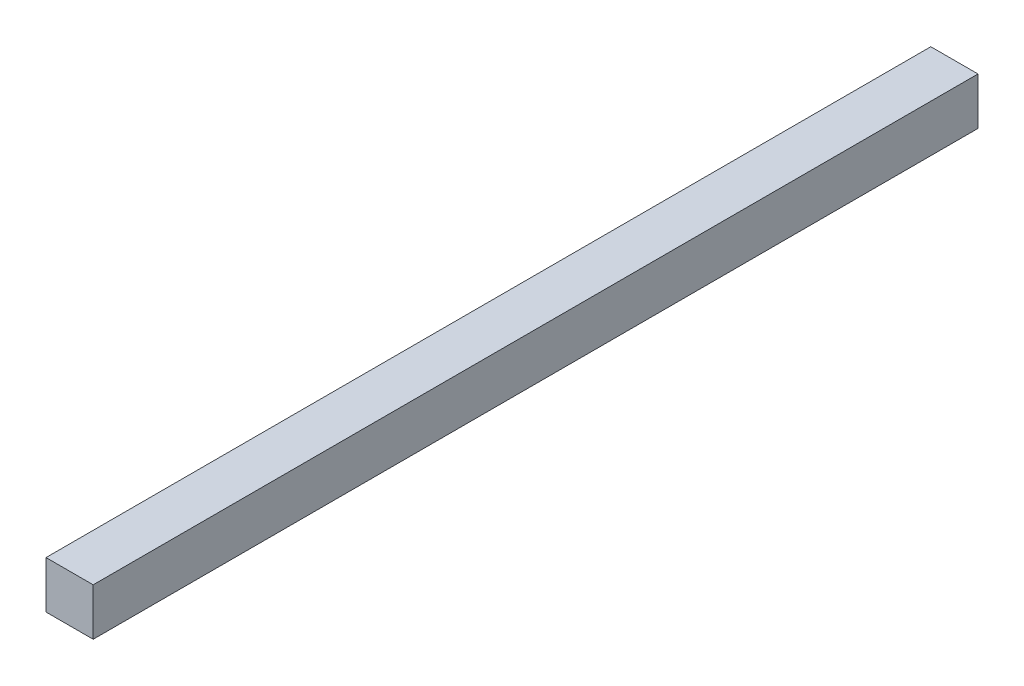
SolidWorks part; units mm, degrees
ref_plane "Płaszczyzna przednia" through (0, 0, 0) normal (0, 0, 1) x (1, 0, 0)
ref_plane "Płaszczyzna górna" through (0, 0, 0) normal (0, 1, 0) x (1, 0, 0)
ref_plane "Płaszczyzna prawa" through (0, 0, 0) normal (1, 0, 0) x (0, 0, -1)
sketch "Szkic1" plane through (0, 0, 0) normal (0, 0, 1) x (1, 0, 0)
  line L1 (0, 0) -> (20, 0)
  line L2 (0, 0) -> (0, 20)
  line L3 (0, 20) -> (20, 20)
  line L4 (20, 0) -> (20, 20)
  dimension "D1" = 20
  dimension "D2" = 20
extrude "Dodanie-wyciągnięcie1" add sketch "Szkic1" against normal blind 375
